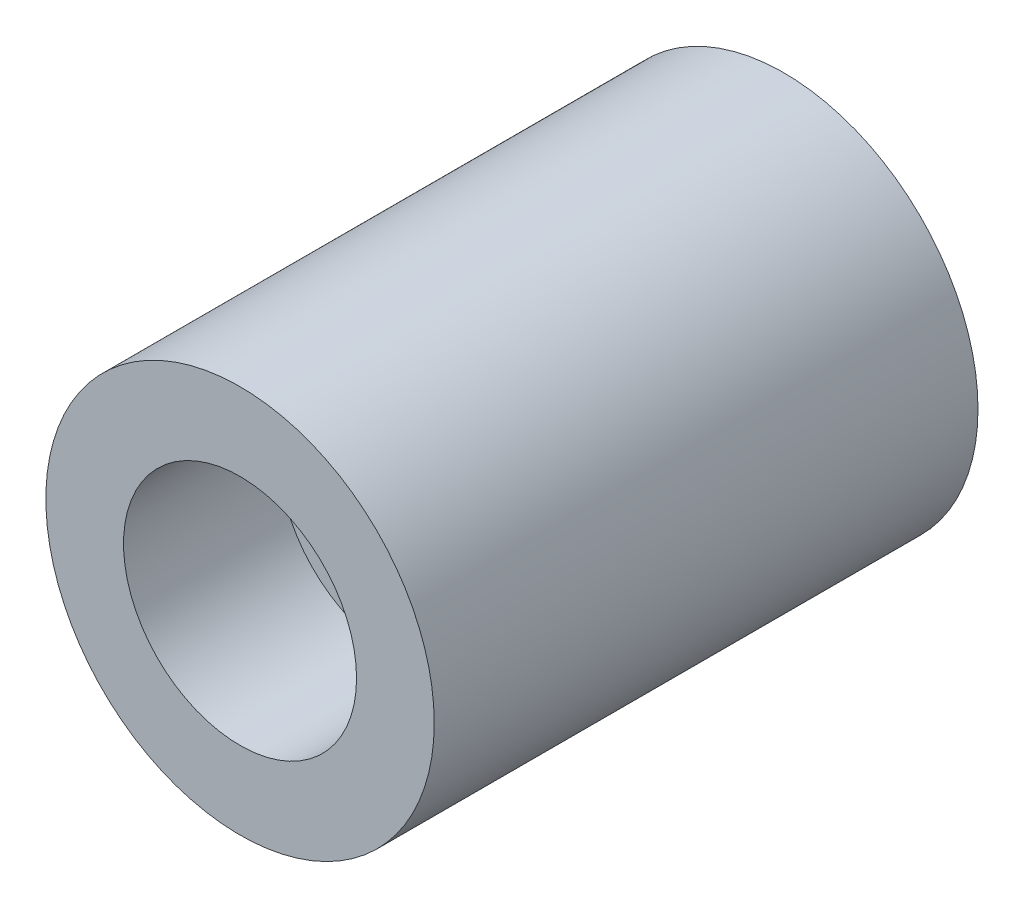
SolidWorks part; units mm, degrees
ref_plane "Front Plane" through (0, 0, 0) normal (0, 0, 1) x (1, 0, 0)
ref_plane "Top Plane" through (0, 0, 0) normal (0, 1, 0) x (1, 0, 0)
ref_plane "Right Plane" through (0, 0, 0) normal (1, 0, 0) x (0, 0, -1)
sketch "Sketch1" plane through (0, 0, 0) normal (0, 1, 0) x (1, 0, 0)
  line L0 (0, 0) -> (0, 3556) construction
  line L1 (0, 3556) -> (1270, 3556)
  line L2 (1270, 3556) -> (1270, 0)
  line L3 (1270, 0) -> (762, 0)
  line L4 (762, 0) -> (762, 1016)
  line L5 (762, 1016) -> (254, 1016)
  line L6 (254, 1016) -> (254, 3048)
  line L7 (254, 3048) -> (0, 3048)
  line L8 (0, 3048) -> (0, 3556)
  dimension "D1" = 3556
  dimension "D2" = 508
  dimension "D3" = 1524
  dimension "D4" = 2540
  dimension "D5" = 3048
  dimension "D6" = 1016
revolve "Revolve1" add sketch "Sketch1" angle 360 about L0
